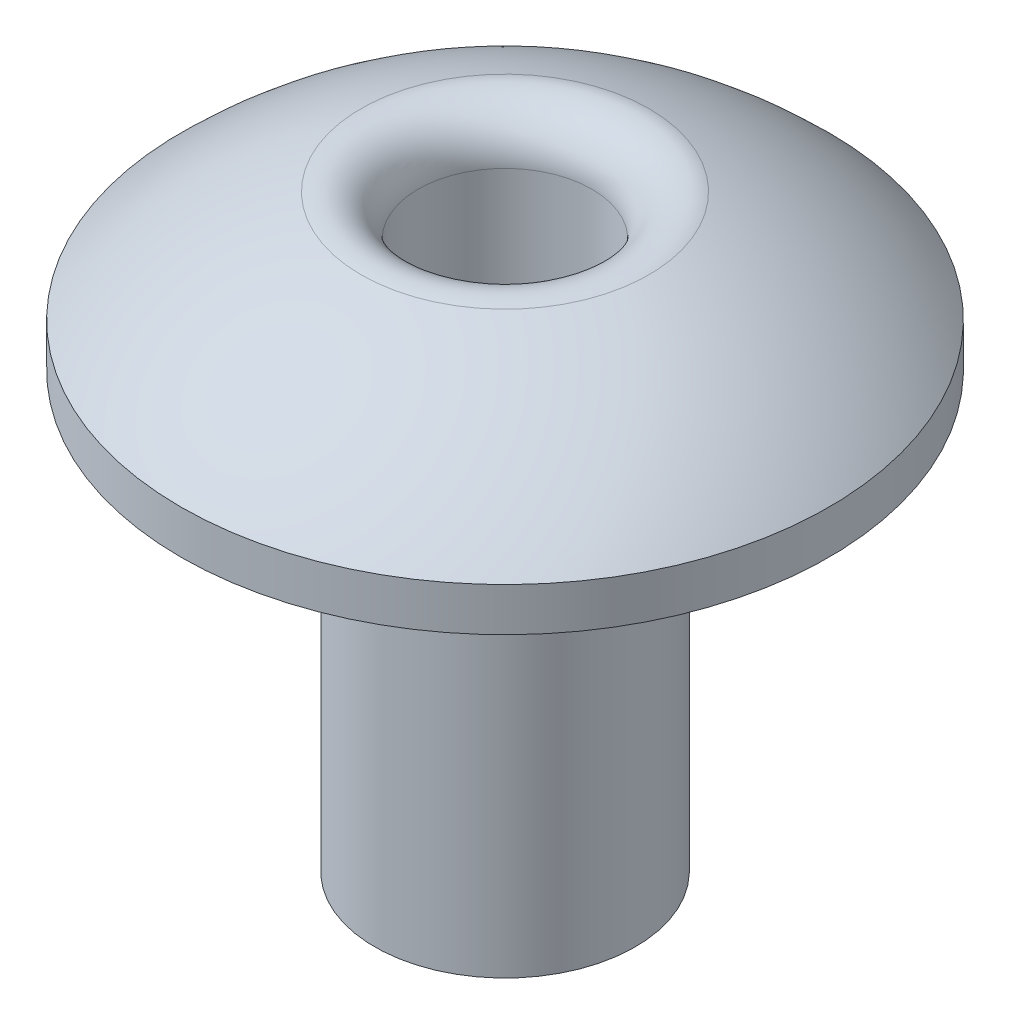
SolidWorks part; units mm, degrees
ref_plane "Front Plane" through (0, 0, 0) normal (0, 0, 1) x (1, 0, 0)
ref_plane "Top Plane" through (0, 0, 0) normal (0, 1, 0) x (1, 0, 0)
ref_plane "Right Plane" through (0, 0, 0) normal (1, 0, 0) x (0, 0, -1)
sketch "Sketch2" plane through (0, 0, 0) normal (1, 0, 0) x (0, 0, -1)
  line L0 (0, 0) -> (-62178.7483, 0) construction
  line L1 (0, 0) -> (0, 62178.7483) construction
  line L3 (0, 1.5453) -> (0, 0)
  line L5 (-3.7307, 0) -> (-3.7307, -0.5)
  line L6 (-3.7307, -0.5) -> (0, -0.5)
  line L7 (0, -0.5) -> (0, 0)
  arc A0 (-3.7307, 0) -> (0, 1.5453) centre (0, -3.7307) cw
  point P8 (0, 0)
  dimension "D1" = 0.5
revolve "Revolve2" add sketch "Sketch2" angle 360 about L7
sketch "Sketch3" plane through (0, -0.5, 0) normal (0, -1, 0) x (1, 0, 0)
  circle A0 centre (0, 0) radius 1.5
  dimension "D1" = 3
extrude "Boss-Extrude1" add sketch "Sketch3" along normal blind 5
sketch "Sketch4" plane through (0, -5.5, 0) normal (0, -1, 0) x (1, 0, 0)
  circle A0 centre (0, 0) radius 1
extrude "Cut-Extrude1" cut sketch "Sketch4" against normal through all
fillet "Fillet1" radius 0.5 1 edges at (0, 1.4497, -1)
scale "ｽｹｰﾙ1" scale about centroid uniform scaling yes scale factor 0.894737
